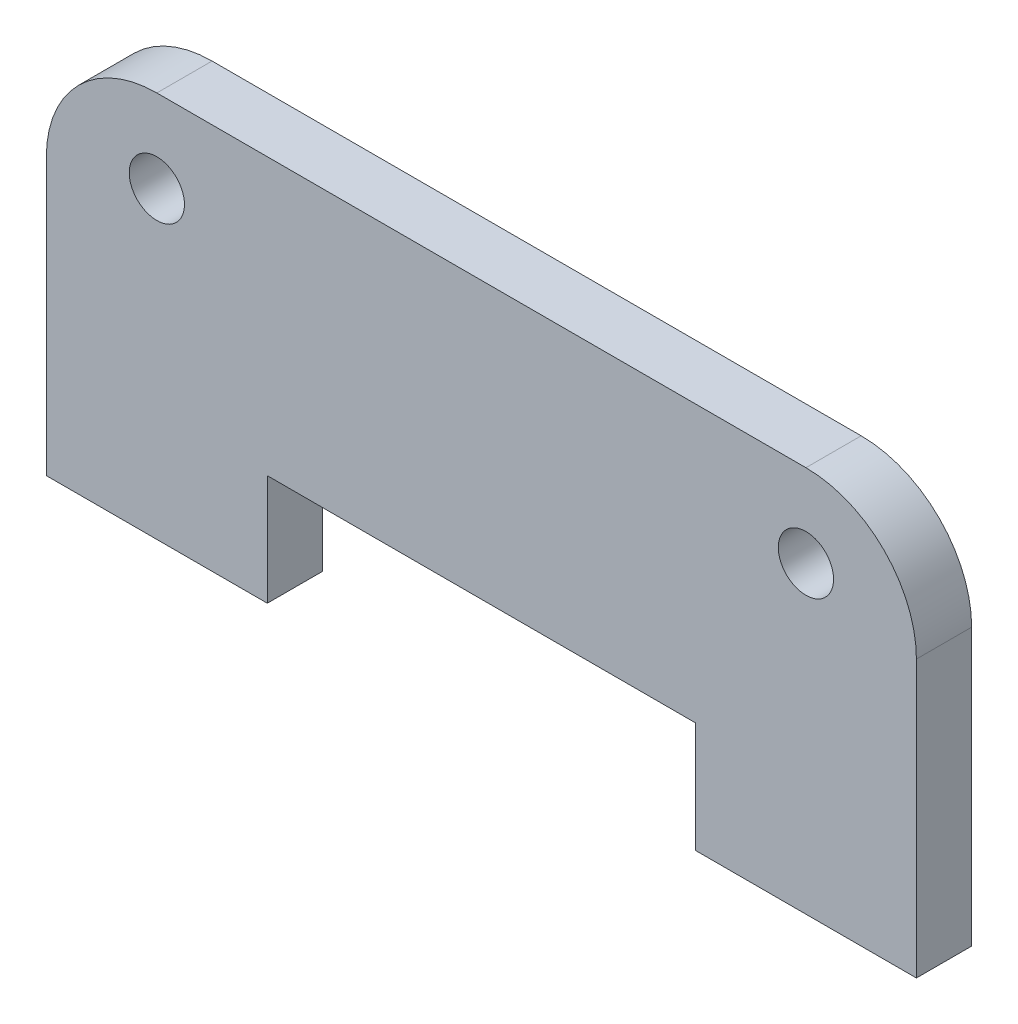
SolidWorks part; units mm, degrees
ref_plane "Front Plane" through (0, 0, 0) normal (0, 0, 1) x (1, 0, 0)
ref_plane "Top Plane" through (0, 0, 0) normal (0, 1, 0) x (1, 0, 0)
ref_plane "Right Plane" through (0, 0, 0) normal (1, 0, 0) x (0, 0, -1)
sketch "Sketch1" plane through (0, 0, 0) normal (0, 0, 1) x (1, 0, 0)
  line L0 (-15.75, -7) -> (-15.75, -11)
  line L1 (-11.75, 3) -> (11.75, 3)
  line L2 (-15.75, -1) -> (-15.75, -7)
  line L3 (-7.75, -7) -> (7.75, -7)
  line L4 (15.75, -1) -> (15.75, -7)
  line L5 (-15.75, -11) -> (-7.75, -11)
  line L6 (-7.75, -11) -> (-7.75, -7)
  line L7 (15.75, -7) -> (15.75, -11)
  line L8 (15.75, -11) -> (7.75, -11)
  line L9 (7.75, -11) -> (7.75, -7)
  circle A0 centre (-11.75, 0) radius 1
  circle A1 centre (11.75, 0) radius 1
  arc A2 (15.75, -1) -> (11.75, 3) centre (11.75, -1) ccw
  arc A3 (-11.75, 3) -> (-15.75, -1) centre (-11.75, -1) ccw
  dimension "D1" = 2
  dimension "D11" = 4
  dimension "D2" = 11.75
  dimension "D3" = 11.75
  dimension "D4" = 4
  dimension "D5" = 4
  dimension "D6" = 3
  dimension "D7" = 7
  dimension "D8" = 4
  dimension "D9" = 8
  dimension "D10" = 4
extrude "Boss-Extrude1" add sketch "Sketch1" along normal blind 2
